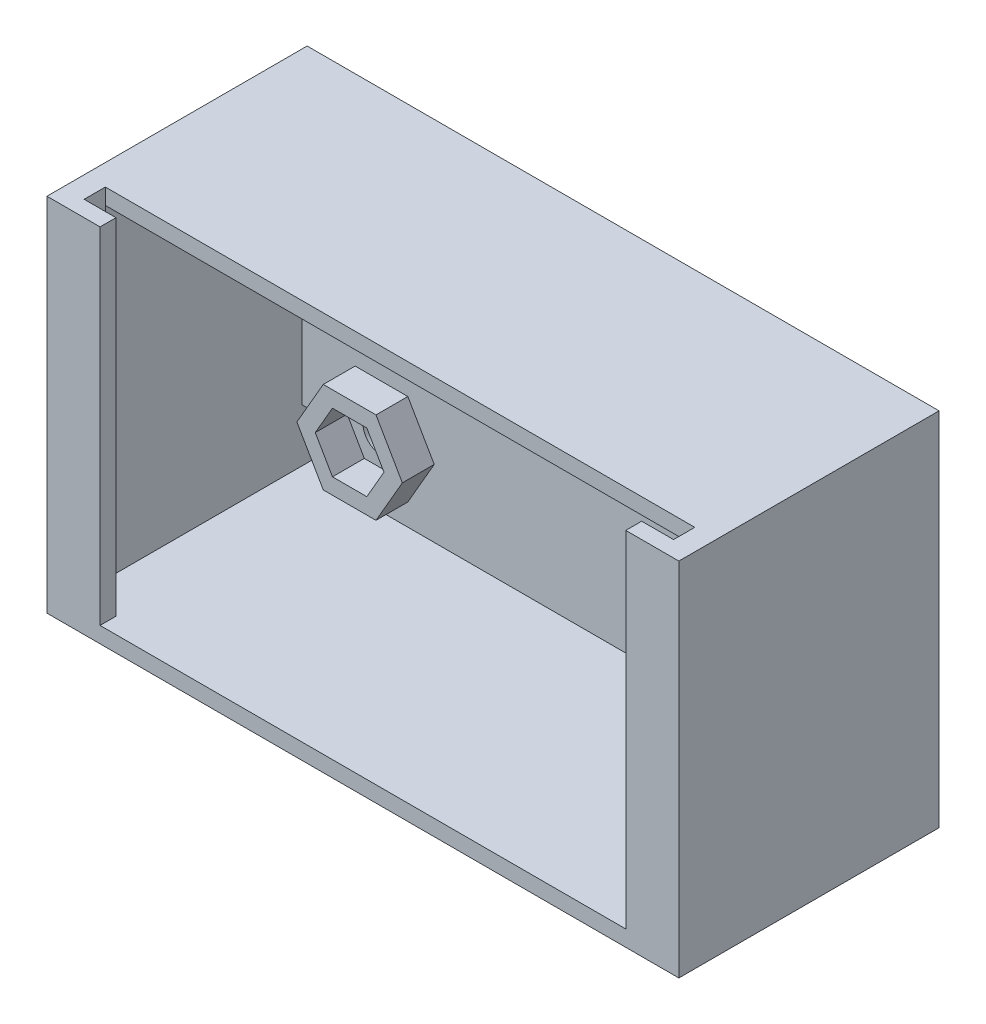
SolidWorks part; units mm, degrees
ref_plane "Alzado" through (0, 0, 0) normal (0, 0, 1) x (1, 0, 0)
ref_plane "Planta" through (0, 0, 0) normal (0, 1, 0) x (1, 0, 0)
ref_plane "Vista lateral" through (0, 0, 0) normal (1, 0, 0) x (0, 0, -1)
sketch "Croquis1" plane through (0, 0, 0) normal (0, 0, 1) x (1, 0, 0)
  line L1 (-28.25, -15.5) -> (28.25, -15.5)
  line L2 (-28.25, -15.5) -> (-28.25, 15.5)
  line L3 (-28.25, 15.5) -> (28.25, 15.5)
  line L4 (28.25, -15.5) -> (28.25, 15.5)
  line L5 (-28.25, -15.5) -> (28.25, 15.5) construction
  line L6 (-28.25, 15.5) -> (28.25, -15.5) construction
  point P0 (0, 0)
  dimension "D1" = 31
  dimension "D2" = 56.5
extrude "Extruir-Lámina1" add sketch "Croquis1" along normal blind 19 thin
sketch "Croquis2" plane through (0, 0, 0) normal (0, 0, -1) x (-1, 0, 0)
  line L4 (-29.75, 17) -> (-29.75, -17)
  line L5 (-29.75, -17) -> (29.75, -17)
  line L6 (29.75, -17) -> (29.75, 17)
  line L7 (29.75, 17) -> (-29.75, 17)
  line L8 (-29.75, 17) -> (-29.75, -17)
  line L9 (-29.75, -17) -> (29.75, -17)
  line L10 (29.75, -17) -> (29.75, 17)
  line L11 (29.75, 17) -> (-29.75, 17)
  dimension "D1" = 0
extrude "Saliente-Extruir1" add sketch "Croquis2" along normal blind 2
sketch "Croquis4" plane through (0, 17, 0) normal (0, 1, 0) x (1, 0, 0)
  line L0 (-29.75, -19) -> (-29.75, -22.5)
  line L1 (-29.75, -22.5) -> (-24.75, -22.5)
  line L2 (-24.75, -22.5) -> (-24.75, -21)
  line L3 (-24.75, -21) -> (-27.75, -21)
  line L4 (-27.75, -21) -> (-27.75, -19)
  line L5 (29.75, -19) -> (-29.75, -19) construction
  line L6 (-27.75, -19) -> (-29.75, -19)
  line L7 (0, -55) -> (0, 55) construction
  line L8 (27.75, -21) -> (27.75, -19)
  line L9 (24.75, -21) -> (27.75, -21)
  line L10 (24.75, -22.5) -> (24.75, -21)
  line L11 (29.75, -22.5) -> (24.75, -22.5)
  line L12 (29.75, -19) -> (29.75, -22.5)
  line L13 (27.75, -19) -> (29.75, -19)
  dimension "D1" = 3.5
  dimension "D2" = 2
  dimension "D3" = 2
  dimension "D4" = 5
extrude "Saliente-Extruir3" add sketch "Croquis4" against normal up to surface (34 mm away) up to face at (0, -17, 8.5)
sketch "Croquis5" plane through (0, 0, 19) normal (0, 0, 1) x (1, 0, 0)
  line L0 (29.75, -17) -> (29.75, 17) construction
  line L1 (-29.75, -17) -> (29.75, -17)
  line L2 (-29.75, -17) -> (-29.75, -15.5)
  line L3 (-29.75, -15.5) -> (29.75, -15.5)
  line L4 (29.75, -17) -> (29.75, -15.5)
  dimension "D1" = 1.5
extrude "Saliente-Extruir4" add sketch "Croquis5" along normal blind 3.5
sketch "Croquis6" plane through (0, 0, 0) normal (0, 0, 1) x (1, 0, 0)
  line L1 (-28.25, -15.5) -> (-23.25, -15.5)
  line L2 (-28.25, -15.5) -> (-28.25, -10.5)
  line L3 (-28.25, -10.5) -> (-23.25, -10.5)
  line L4 (-23.25, -15.5) -> (-23.25, -10.5)
  dimension "D1" = 5
  dimension "D2" = 5
extrude "Cortar-Extruir1" cut sketch "Croquis6" against normal blind 3.5
sketch "Croquis7" plane through (0, 0, -2) normal (0, 0, -1) x (-1, 0, 0)
  line L0 (-1.75, 17) -> (-1.75, -17) construction
  line L1 (29.75, 17) -> (-29.75, 17) construction
  line L2 (-29.75, -17) -> (29.75, -17) construction
  line L3 (29.75, -17) -> (29.75, 17) construction
  line L4 (24.75, -15.5) -> (27.75, -15.5) construction
  circle A0 centre (20.75, 12.11) radius 1.75
  circle A1 centre (20.75, -9.14) radius 1.75
  circle A2 centre (-24.25, -9.14) radius 1.75
  circle A3 centre (-24.25, 12.11) radius 1.75
  dimension "D2" = 3.5
  dimension "D3" = 3.5
  dimension "D1" = 21.25
  dimension "D4" = 22.5
  dimension "D5" = 6.36
  dimension "D6" = 31.5
extrude "Cortar-Extruir2" cut sketch "Croquis7" against normal blind 3.5
sketch "Croquis8" plane through (0, 0, 0) normal (0, 0, 1) x (1, 0, 0)
  line L1 (-17.5168, 12.11) -> (-19.1334, 14.91)
  line L2 (-19.1334, 14.91) -> (-22.3666, 14.91)
  line L3 (-22.3666, 14.91) -> (-23.9832, 12.11)
  line L4 (-23.9832, 12.11) -> (-22.3666, 9.31)
  line L5 (-22.3666, 9.31) -> (-19.1334, 9.31)
  line L6 (-19.1334, 9.31) -> (-17.5168, 12.11)
  line L7 (27.4832, 12.11) -> (25.8666, 14.91)
  line L8 (25.8666, 14.91) -> (22.6334, 14.91)
  line L9 (22.6334, 14.91) -> (21.0168, 12.11)
  line L10 (21.0168, 12.11) -> (22.6334, 9.31)
  line L11 (22.6334, 9.31) -> (25.8666, 9.31)
  line L12 (25.8666, 9.31) -> (27.4832, 12.11)
  line L13 (-17.5168, -9.14) -> (-19.1334, -6.34)
  line L14 (-19.1334, -6.34) -> (-22.3666, -6.34)
  line L15 (-22.3666, -6.34) -> (-23.9832, -9.14)
  line L16 (-23.9832, -9.14) -> (-22.3666, -11.94)
  line L17 (-22.3666, -11.94) -> (-19.1334, -11.94)
  line L18 (-19.1334, -11.94) -> (-17.5168, -9.14)
  line L19 (27.4832, -9.14) -> (25.8666, -6.34)
  line L20 (25.8666, -6.34) -> (22.6334, -6.34)
  line L21 (22.6334, -6.34) -> (21.0168, -9.14)
  line L22 (21.0168, -9.14) -> (22.6334, -11.94)
  line L23 (22.6334, -11.94) -> (25.8666, -11.94)
  line L24 (25.8666, -11.94) -> (27.4832, -9.14)
  circle A0 centre (-20.75, 12.11) radius 2.8 construction
  circle A1 centre (24.25, 12.11) radius 2.8 construction
  circle A2 centre (-20.75, -9.14) radius 2.8 construction
  circle A3 centre (24.25, -9.14) radius 2.8 construction
  dimension "D1" = 5.6
  dimension "D2" = 5.6
  dimension "D3" = 5.6
  dimension "D4" = 5.6
extrude "Extruir-Lámina2" add sketch "Croquis8" along normal blind 3 thin
